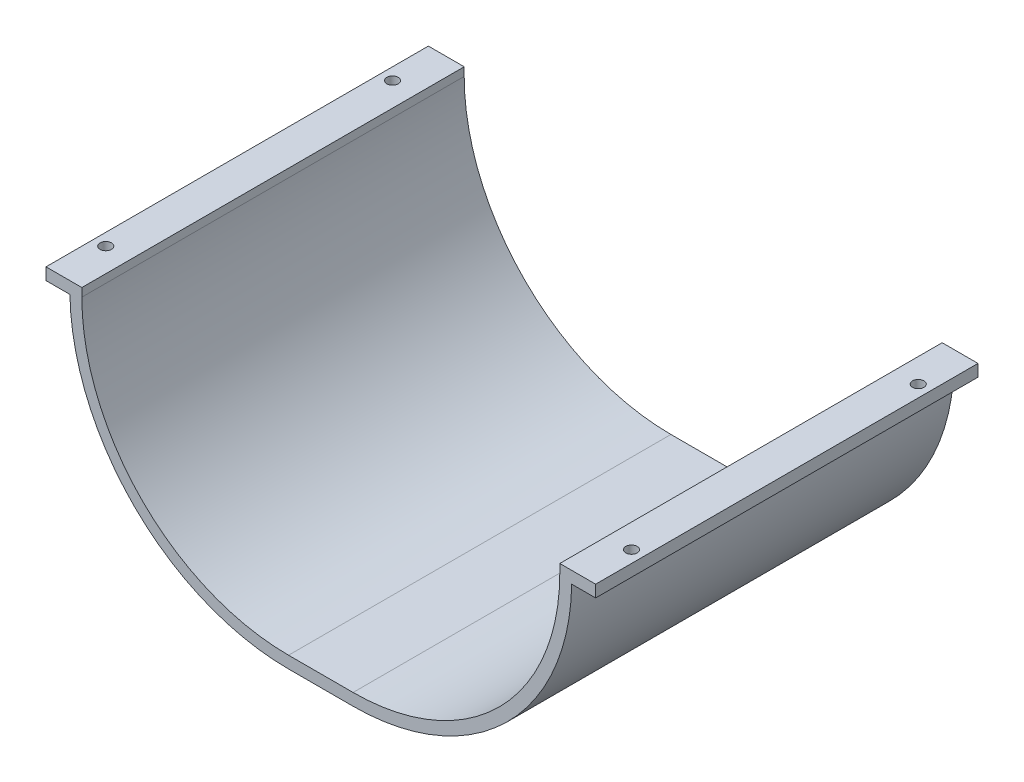
SolidWorks part; units mm, degrees
ref_plane "Front Plane" through (0, 0, 0) normal (0, 0, 1) x (1, 0, 0)
ref_plane "Top Plane" through (0, 0, 0) normal (0, 1, 0) x (1, 0, 0)
ref_plane "Right Plane" through (0, 0, 0) normal (1, 0, 0) x (0, 0, -1)
sketch "Sketch1" plane through (0, 0, 0) normal (0, 0, 1) x (1, 0, 0)
  line L1 (86.5, 0) -> (113.5, 0)
  line L2 (0, 86.5) -> (0, 90)
  line L4 (200, 86.5) -> (200, 90)
  line L5 (205, 86.5) -> (205, 90)
  line L6 (86.5, -5) -> (113.5, -5)
  line L7 (-5, 86.5) -> (-5, 90)
  line L8 (-5, 90) -> (205, 90)
  line L9 (-5, 90) -> (-5, 87.5488)
  line L10 (-5, 85) -> (-4.9791, 85)
  line L11 (-5, 90) -> (-15, 90)
  line L12 (-5, 90) -> (-5, 86.5)
  line L13 (-5, 85) -> (-15, 85)
  line L14 (-15, 90) -> (-15, 85)
  line L15 (205, 85) -> (204.9608, 85)
  line L16 (205, 90) -> (215, 90)
  line L17 (205, 90) -> (205, 86.5)
  line L18 (205, 85) -> (215, 85)
  line L19 (215, 90) -> (215, 85)
  arc A0 (113.5, 0) -> (200, 86.5) centre (113.5, 86.5) ccw
  arc A1 (86.5, 0) -> (0, 86.5) centre (86.5, 86.5) cw
  arc A2 (113.5, -5) -> (205, 86.5) centre (113.5, 86.5) ccw
  arc A3 (86.5, -5) -> (-5, 86.5) centre (86.5, 86.5) cw
  point P10 (200, 0)
  point P13 (0, 0)
  dimension "D4" = 86.5
  dimension "D1" = 5
  dimension "D2" = 10
  dimension "D3" = 5
  dimension "D5" = 10
extrude "Boss-Extrude1" add sketch "Sketch1" along normal blind 160
sketch "Sketch2" plane through (0, 85, 0) normal (0, -1, 0) x (1, 0, 0)
  line L0 (-9.9939, 0) -> (-9.9939, 160)
  line L1 (-15, 0) -> (-4.9877, 0) construction
  line L2 (-15, 160) -> (-4.9877, 160) construction
  line L3 (209.9939, 160) -> (209.9939, 0)
  line L4 (215, 160) -> (204.9877, 160) construction
  line L5 (215, 0) -> (204.9877, 0) construction
  circle A0 centre (-9.9939, 20) radius 2.3813
  circle A1 centre (-9.9939, 140) radius 2.3813
  circle A2 centre (209.9939, 140) radius 2.3813
  circle A3 centre (209.9939, 20) radius 2.3813
  dimension "D1" = 4.7625
  dimension "D2" = 4.7625
  dimension "D3" = 4.7625
  dimension "D4" = 4.7625
  dimension "D5" = 20
  dimension "D6" = 20
  dimension "D7" = 20
  dimension "D8" = 20
extrude "Cut-Extrude1" cut sketch "Sketch2" against normal blind 160 contours L0 A1 | L0 A1 | A0 | A3 | A2
